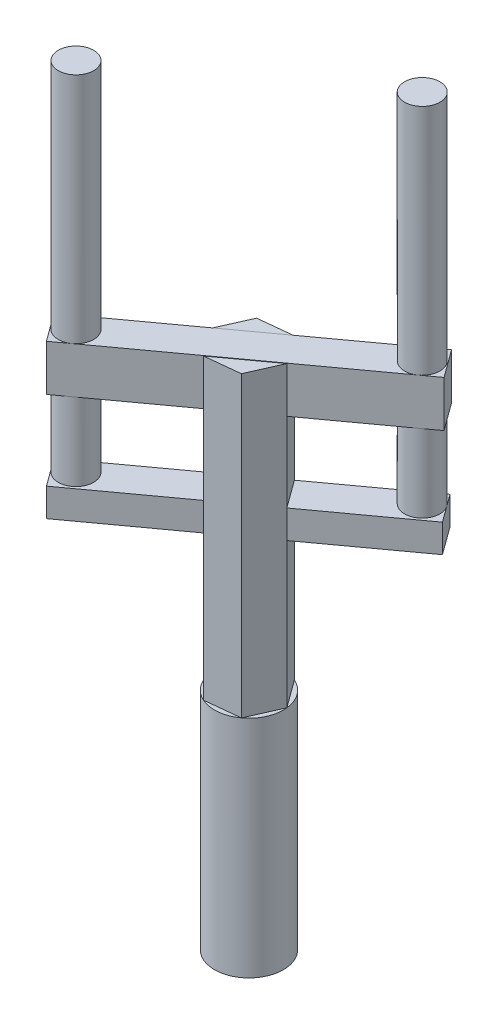
SolidWorks part; units mm, degrees
ref_plane "Спереди" through (0, 0, 0) normal (0, 0, 1) x (1, 0, 0)
ref_plane "Сверху" through (0, 0, 0) normal (0, 1, 0) x (1, 0, 0)
ref_plane "Справа" through (0, 0, 0) normal (1, 0, 0) x (0, 0, -1)
sketch "Эскиз1" plane through (0, 0, 0) normal (0, 1, 0) x (1, 0, 0)
  line L1 (18.0142, -24.7586) -> (30.4487, 3.2215)
  line L2 (30.4487, 3.2215) -> (12.4345, 27.98)
  line L3 (12.4345, 27.98) -> (-18.0142, 24.7586)
  line L4 (-18.0142, 24.7586) -> (-30.4487, -3.2215)
  line L5 (-30.4487, -3.2215) -> (-12.4345, -27.98)
  line L6 (-12.4345, -27.98) -> (18.0142, -24.7586)
  circle A0 centre (0, 0) radius 26.5165 construction
extrude "Бобышка-Вытянуть1" add sketch "Эскиз1" along normal blind 265
sketch "Эскиз3" plane through (21.4416, 0, -15.6007) normal (0.8086, 0, -0.5883) x (-0.5883, 0, -0.8086)
  line L0 (-15.3093, 265) -> (-15.3093, 0) construction
  line L1 (15.3093, 265.3664) -> (-15.3093, 265.3664)
  line L2 (15.3093, 265.3664) -> (15.3093, 224.4233)
  line L3 (15.3093, 224.4233) -> (-15.3093, 224.4233)
  line L4 (-15.3093, 265.3664) -> (-15.3093, 224.4233)
  line L5 (15.3093, 265.3664) -> (-15.3093, 224.4233) construction
  line L6 (15.3093, 224.4233) -> (-15.3093, 265.3664) construction
  point P0 (0, 244.8948)
extrude "Бобышка-Вытянуть2" add sketch "Эскиз3" along normal blind 100 and the other way blind 153
sketch "Эскиз5" plane through (0, 265.3664, 0) normal (0, 1, 0) x (1, 0, 0)
  line L0 (-8.9938, 12.389) -> (9.0204, -12.3696) construction
  line L1 (-111.2833, -62.0362) -> (93.2957, 86.8142) construction
  line L2 (-93.2691, -86.7948) -> (111.3099, 62.0556) construction
  circle A0 centre (-89.323, -64.4781) radius 15.7239
  circle A1 centre (88.8618, 65.168) radius 15.7239
extrude "Бобышка-Вытянуть3" add sketch "Эскиз5" along normal blind 207 and the other way blind 110
sketch "Эскиз7" plane through (21.4416, 0, -15.6007) normal (0.8086, 0, -0.5883) x (-0.5883, 0, -0.8086)
  line L0 (-15.3093, 224.4233) -> (-15.3093, 0) construction
  line L1 (-15.3093, 153.8404) -> (15.3093, 153.8404)
  line L2 (-15.3093, 153.8404) -> (-15.3093, 128.7649)
  line L3 (-15.3093, 128.7649) -> (15.3093, 128.7649)
  line L4 (15.3093, 153.8404) -> (15.3093, 128.7649)
  line L5 (15.3093, 224.4233) -> (15.3093, 0) construction
extrude "Бобышка-Вытянуть4" add sketch "Эскиз7" along normal blind 99 and the other way blind 153
sketch "Эскиз8" plane through (0, 0, 0) normal (0, -1, 0) x (1, 0, 0)
  circle A0 centre (0, 0) radius 30.6186
extrude "Бобышка-Вытянуть5" add sketch "Эскиз8" along normal blind 200
